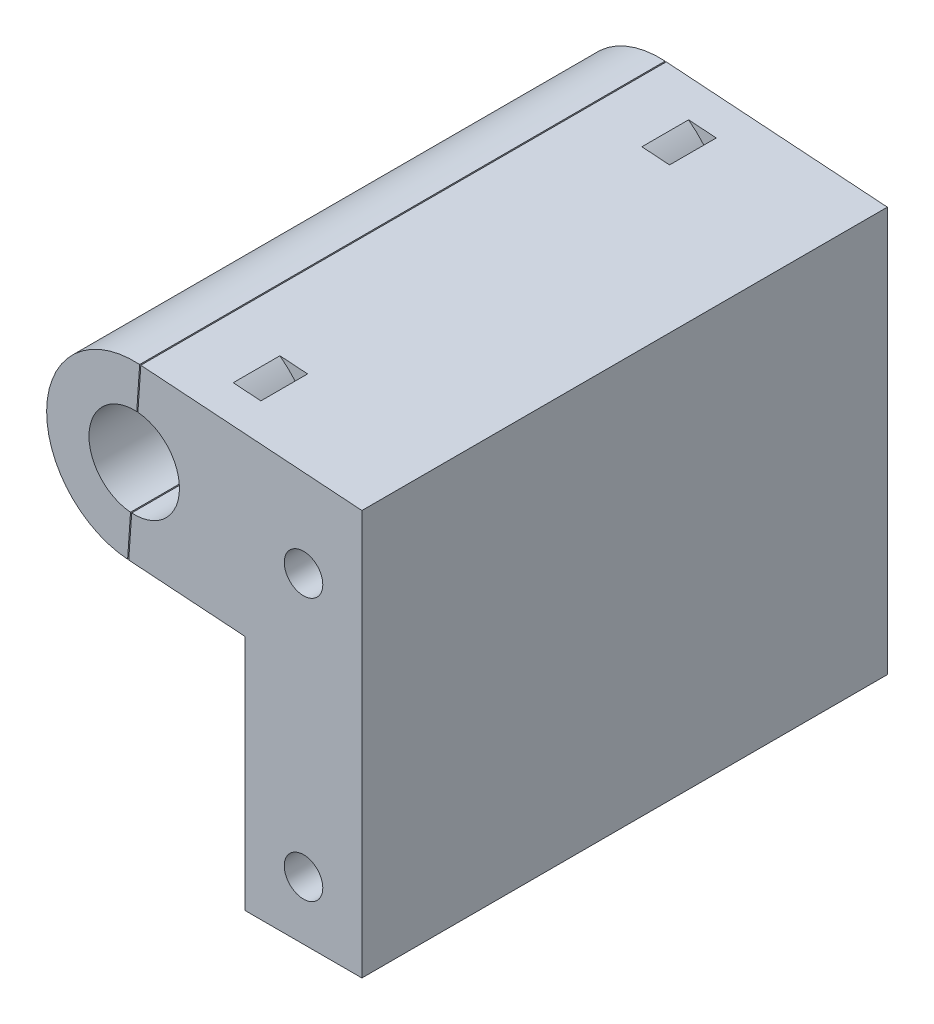
SolidWorks part; units mm, degrees
ref_plane "Front Plane" through (0, 0, 0) normal (0, 0, 1) x (1, 0, 0)
ref_plane "Top Plane" through (0, 0, 0) normal (0, 1, 0) x (1, 0, 0)
ref_plane "Right Plane" through (0, 0, 0) normal (1, 0, 0) x (0, 0, -1)
sketch "Sketch1" plane through (0, 0, 0) normal (0, 0, 1) x (1, 0, 0)
  line L0 (-182, 170) -> (-167.5, 169) construction
  line L1 (-167.5, 169) -> (-167.5, 146.5) construction
  line L2 (-182.516, 162.5178) -> (-172.5, 161.827)
  line L3 (-172.5, 161.827) -> (-172.5, 141.5)
  line L4 (-181.484, 177.4822) -> (-162.5, 176.173)
  line L5 (-162.5, 176.173) -> (-162.5, 141.5)
  line L6 (-172.5, 141.5) -> (-162.5, 141.5)
  line L7 (-167.5, 146.5) -> (-167.5, 141.5) construction
  circle A0 centre (-167.5, 146.5) radius 2.4 construction
  circle A3 centre (-167.5, 146.5) radius 2.4 construction
  circle A4 centre (-167.5, 169) radius 2.4 construction
  arc A5 (-182.516, 162.5178) -> (-181.484, 177.4822) centre (-182, 170) ccw
  dimension "D1" = 7.5
  dimension "D6" = 4.8
  dimension "D3" = 5
  dimension "D4" = 14.5
  dimension "D5" = 23.5
  dimension "D2" = 22.5
  dimension "D7" = 5
  dimension "D8" = 7.5
  dimension "D9" = 5
extrude "Boss-Extrude1" add sketch "Sketch1" along normal blind 45 contours L5 L6 L3 L2 A5 L4
sketch "Sketch2" plane through (0, 0, 0) normal (0, 0, -1) x (-1, 0, 0)
  line L0 (162.5, 176.173) -> (181.484, 177.4822) construction
  line L2 (182.516, 162.5178) -> (172.5, 161.827) construction
  arc A0 (176.5208, 177.1399) -> (177.5529, 162.1755) centre (182, 170) ccw
  arc A1 (181.484, 177.4822) -> (182.516, 162.5178) centre (182, 170) ccw construction
  arc A3 (175.6076, 178.3299) -> (176.8117, 160.8714) centre (182, 170) ccw
  arc A4 (176.5208, 177.1399) -> (175.6076, 178.3299) centre (176.0642, 177.7349) ccw
  arc A5 (177.5529, 162.1755) -> (176.8117, 160.8714) centre (177.1823, 161.5234) cw
  point P8 (177.508, 162.1724)
  point P9 (0, 0)
  point P10 (0, 0)
  point P11 (182.1468, 160.2513)
  point P17 (0, 0)
  dimension "D1" = 9
  dimension "D2" = 1.5
extrude "Cut-Extrude1" cut sketch "Sketch2" against normal mid plane 4 from offset 5 offset against normal yes
ref_plane "Plane1" through (0, 0, 22.5) normal (0, 0, -1) x (-1, 0, 0)
mirror "Mirror1" about plane through (0, 0, 22.5) normal (0, 0, -1) of "Cut-Extrude1"
hole_wizard "M4x0.7 Tapped Hole1" positions "Sketch3" profile "Sketch4" tap size "M4x0.7" standard "ANSI Metric" end condition through all
sketch "Sketch3" plane through (0, 0, 45) normal (0, 0, 1) x (1, 0, 0)
  point P0 (-167.5, 169)
  point P3 (-167.5, 146.5)
sketch "Sketch4" plane through (-167.5, 169, 45) normal (1, 0, 0) x (0, -1, 0)
  line L0 (0, 0) -> (0, 45)
  line L1 (0, 45) -> (1.65, 45)
  line L2 (1.65, 45) -> (1.65, 0)
  line L5 (1.65, 0) -> (0, 0)
  line L11 (0, -6.35) -> (0, 107.95) construction
  dimension "Thru Tap Drill Dia." = 3.3
  dimension "Thru Tap Drill Depth" = 45
cosmetic thread "Hole Thread1" parameters "D2"=4
cosmetic thread "Hole Thread2" parameters "D2"=4
sketch "Sketch5" plane through (0, 0, 45) normal (0, 0, 1) x (1, 0, 0)
  circle A0 centre (-182, 170) radius 7.5
extrude "Boss-Extrude2" add sketch "Sketch5" against normal through all
sketch "Sketch6" plane through (0, 0, 45) normal (0, 0, 1) x (1, 0, 0)
  circle A0 centre (-182, 170) radius 3.875
  dimension "D1" = 7.75
extrude "Cut-Extrude2" cut sketch "Sketch6" against normal through all
sketch "Sketch7" plane through (0, 0, 0) normal (0, 0, -1) x (-1, 0, 0)
  line L0 (181.4341, 177.4788) -> (182.4661, 162.5143)
  line L1 (181.4341, 177.4788) -> (181.5339, 177.4857)
  line L2 (182.4661, 162.5143) -> (182.5659, 162.5212)
  line L3 (181.5339, 177.4857) -> (182.5659, 162.5212)
  line L4 (162.5, 176.173) -> (181.484, 177.4822) construction
  line L5 (182.516, 162.5178) -> (172.5, 161.827) construction
  line L6 (182.516, 162.5178) -> (181.484, 177.4822) construction
  point P10 (181.484, 177.4822)
  dimension "D1" = 0.1
extrude "Cut-Extrude3" cut sketch "Sketch7" against normal through all
